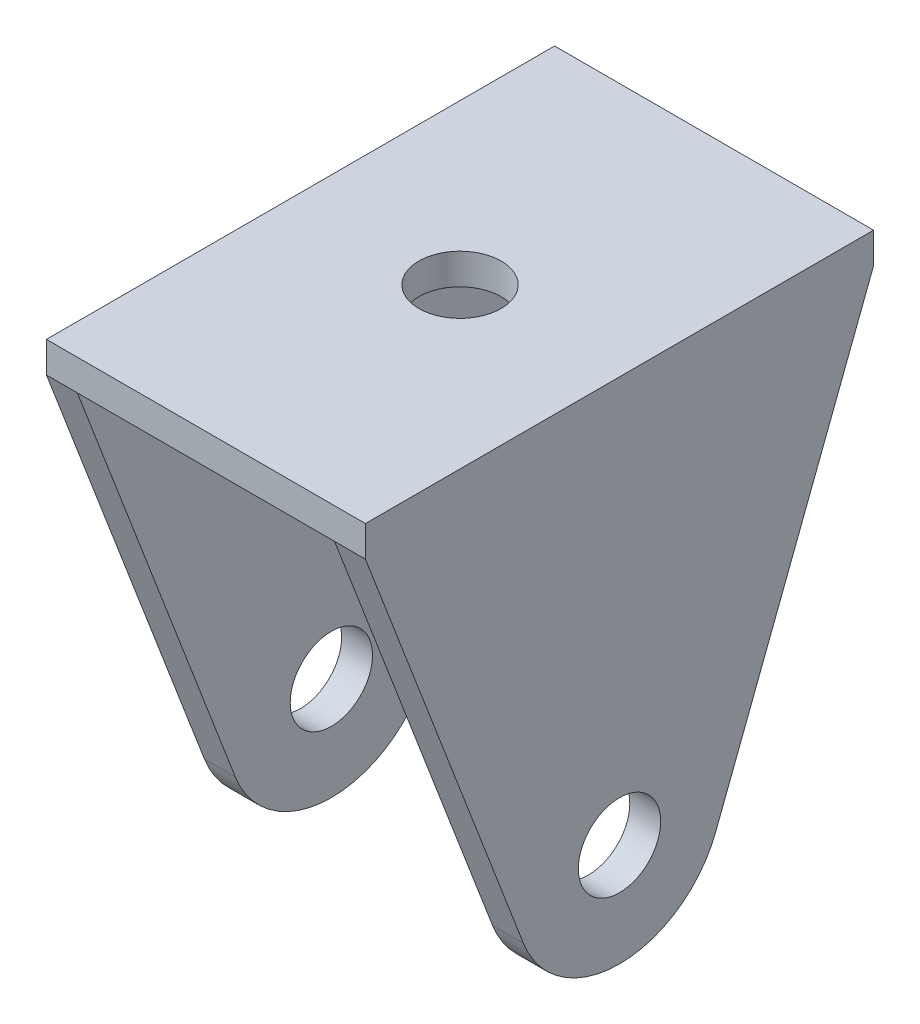
SolidWorks part; units mm, degrees
ref_plane "Alzado" through (0, 0, 0) normal (0, 0, 1) x (1, 0, 0)
ref_plane "Planta" through (0, 0, 0) normal (0, 1, 0) x (1, 0, 0)
ref_plane "Vista lateral" through (0, 0, 0) normal (1, 0, 0) x (0, 0, -1)
sketch "Croquis1" plane through (0, 0, 0) normal (1, 0, 0) x (0, 0, -1)
  line L0 (-9.3358, -3.5837) -> (-24.6904, 36.4163)
  line L1 (-24.6904, 36.4163) -> (24.6904, 36.4163)
  line L2 (24.6904, 36.4163) -> (9.3358, -3.5837)
  line L3 (0, 0) -> (0, 36.4163) construction
  circle A0 centre (0, 0) radius 4
  circle A1 centre (0, 0) radius 30 construction
  arc A2 (-9.3358, -3.5837) -> (9.3358, -3.5837) centre (0, 0) ccw
  dimension "D1" = 8
  dimension "D2" = 60
  dimension "D3" = 20
  dimension "D4" = 40
  dimension "D5" = 21
extrude "Saliente-Extruir1" add sketch "Croquis1" along normal blind 3
ref_plane "Plano1" through (-25, 0, 0) normal (-1, 0, 0) x (0, 0, 1)
sketch "Croquis2" plane through (-25, 0, 0) normal (-1, 0, 0) x (0, 0, 1)
  line L3 (9.3358, -3.5837) -> (24.6904, 36.4163)
  line L4 (24.6904, 36.4163) -> (-24.6904, 36.4163)
  line L5 (-24.6904, 36.4163) -> (-9.3358, -3.5837)
  line L6 (9.3358, -3.5837) -> (24.6904, 36.4163)
  line L7 (24.6904, 36.4163) -> (-24.6904, 36.4163)
  line L8 (-24.6904, 36.4163) -> (-9.3358, -3.5837)
  circle A0 centre (0, 0) radius 4 construction
  arc A1 (-9.3358, -3.5837) -> (9.3358, -3.5837) centre (0, 0) ccw
  arc A2 (-9.3358, -3.5837) -> (9.3358, -3.5837) centre (0, 0) ccw
  circle A3 centre (0, 0) radius 4
  dimension "D1" = 0
extrude "Saliente-Extruir2" add sketch "Croquis2" along normal blind 3 separate body
sketch "Croquis3" plane through (0, 36.4163, 0) normal (0, 1, 0) x (1, 0, 0)
  line L1 (-28, 24.6904) -> (3, 24.6904)
  line L2 (-28, 24.6904) -> (-28, -24.6904)
  line L3 (-28, -24.6904) -> (3, -24.6904)
  line L4 (3, 24.6904) -> (3, -24.6904)
extrude "Saliente-Extruir3" add sketch "Croquis3" along normal blind 3
sketch "Croquis5" plane through (0, 39.4163, 0) normal (0, 1, 0) x (1, 0, 0)
  line L0 (-12.5, 24.6904) -> (-12.5, -24.6904) construction
  line L1 (3, 24.6904) -> (-28, 24.6904) construction
  line L2 (-28, -24.6904) -> (3, -24.6904) construction
  line L3 (-28, 0) -> (3, 0) construction
  line L4 (-28, 24.6904) -> (-28, -24.6904) construction
  line L5 (3, -24.6904) -> (3, 24.6904) construction
  circle A0 centre (-12.5, 0) radius 4
  dimension "D1" = 8
extrude "Cortar-Extruir1" cut sketch "Croquis5" against normal blind 3
